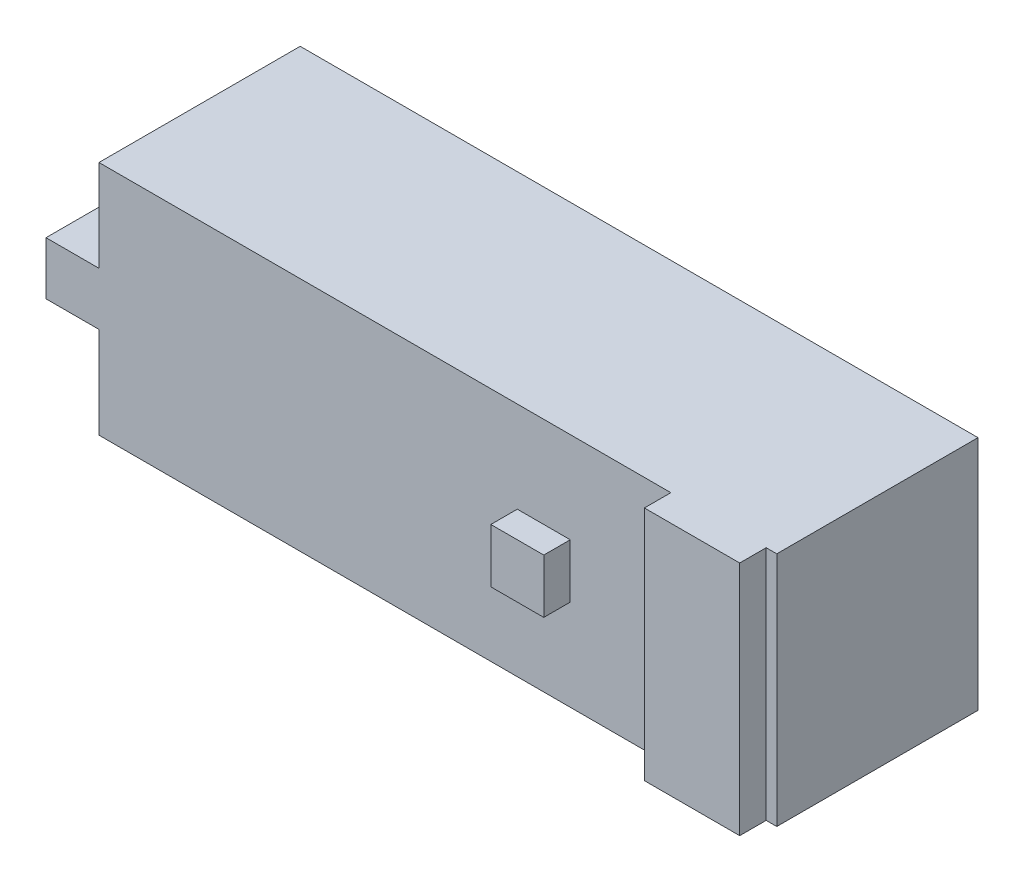
SolidWorks part; units mm, degrees
ref_plane "Front Plane" through (0, 0, 0) normal (0, 0, 1) x (1, 0, 0)
ref_plane "Top Plane" through (0, 0, 0) normal (0, 1, 0) x (1, 0, 0)
ref_plane "Right Plane" through (0, 0, 0) normal (1, 0, 0) x (0, 0, -1)
sketch "Sketch1" plane through (0, 0, 0) normal (0, 0, 1) x (1, 0, 0)
  line L0 (-32, 2.5) -> (-37, 2.5) construction
  line L1 (-32, 11.15) -> (32, 11.15) construction
  line L2 (-32, 11.15) -> (-32, -11.15) construction
  line L3 (-32, -11.15) -> (32, -11.15) construction
  line L4 (32, 11.15) -> (32, -11.15) construction
  line L5 (-32, 11.15) -> (32, -11.15) construction
  line L6 (-32, -11.15) -> (32, 11.15) construction
  line L7 (-23, 1.825) -> (-19, 1.825) construction
  line L8 (-23, 1.825) -> (-23, -1.825) construction
  line L9 (-23, -1.825) -> (-19, -1.825) construction
  line L10 (-19, 1.825) -> (-19, -1.825) construction
  line L11 (-23, 1.825) -> (-19, -1.825) construction
  line L12 (-23, -1.825) -> (-19, 1.825) construction
  line L13 (0, 0) -> (-44.9642, 0) construction
  line L14 (-32, -2.5) -> (-37, -2.5) construction
  line L15 (-37, 2.5) -> (-37, -2.5) construction
  line L16 (31, 11.15) -> (31, -11.15) construction
  line L17 (7.5, 2.55) -> (12.5, 2.55)
  line L18 (7.5, 2.55) -> (7.5, -2.55)
  line L19 (7.5, -2.55) -> (12.5, -2.55)
  line L20 (12.5, 2.55) -> (12.5, -2.55)
  line L21 (7.5, 2.55) -> (12.5, -2.55) construction
  line L22 (7.5, -2.55) -> (12.5, 2.55) construction
  line L23 (22, 11.15) -> (22, -11.15) construction
  circle A0 centre (-21, 0) radius 2.7075 construction
  circle A1 centre (-10, 0) radius 2.1
  point P0 (0, 0)
  point P6 (-21, 0)
  point P21 (10, 0)
  dimension "D8" = 4.2
  dimension "D1" = 64
  dimension "D2" = 22.3
  dimension "D3" = 11
  dimension "D4" = 3.65
  dimension "D5" = 4
  dimension "D6" = 2.5
  dimension "D7" = 5
  dimension "D9" = 11
  dimension "D10" = 20
  dimension "D11" = 5.1
  dimension "D12" = 5
  dimension "D13" = 63
  dimension "D14" = 9
sketch "Sketch2" plane through (0, 0, 0) normal (0, 0, 1) x (1, 0, 0)
  line L0 (-32, 11.15) -> (32, 11.15) construction
  line L1 (-32, 11.15) -> (-32, -11.15) construction
  line L2 (-32, -11.15) -> (32, -11.15) construction
  line L3 (32, 11.15) -> (32, -11.15) construction
  line L4 (-32, 11.15) -> (32, 11.15)
  line L5 (-32, 11.15) -> (-32, -11.15)
  line L6 (-32, -11.15) -> (32, -11.15)
  line L7 (32, 11.15) -> (32, -11.15)
  line L8 (-32, 2.5) -> (-37, 2.5) construction
  line L9 (-37, 2.5) -> (-37, -2.5) construction
  line L10 (-32, -2.5) -> (-37, -2.5) construction
  line L11 (-32, 2.5) -> (-37, 2.5)
  line L12 (-37, 2.5) -> (-37, -2.5)
  line L13 (-32, -2.5) -> (-37, -2.5)
extrude "Boss-Extrude1" add sketch "Sketch2" along normal blind 19 contours L7 L4 L5 L6 | L13 L5 L11 L12
sketch "Sketch3" plane through (0, 0, 0) normal (0, 0, 1) x (1, 0, 0)
  line L0 (-23, -1.825) -> (-19, -1.825) construction
  line L1 (-23, 1.825) -> (-19, 1.825) construction
  line L2 (-23, -1.825) -> (-19, -1.825)
  line L3 (-23, 1.825) -> (-19, 1.825)
  circle A0 centre (-21, 0) radius 2.7075 construction
  circle A1 centre (-21, 0) radius 2.7075
extrude "Boss-Extrude2" add sketch "Sketch3" against normal blind 8 contours L3 A1 L2
sketch "Sketch4" plane through (0, 0, 0) normal (0, 0, -1) x (-1, 0, 0)
  line L0 (-7.5, 2.55) -> (-12.5, 2.55) construction
  line L1 (-7.5, 2.55) -> (-7.5, -2.55) construction
  line L2 (-7.5, -2.55) -> (-12.5, -2.55) construction
  line L3 (-12.5, 2.55) -> (-12.5, -2.55) construction
  line L4 (-7.5, 2.55) -> (-12.5, 2.55)
  line L5 (-7.5, 2.55) -> (-7.5, -2.55)
  line L6 (-7.5, -2.55) -> (-12.5, -2.55)
  line L7 (-12.5, 2.55) -> (-12.5, -2.55)
  circle A0 centre (10, 0) radius 2.1 construction
  circle A1 centre (10, 0) radius 2.1
extrude "Boss-Extrude3" add sketch "Sketch4" along normal blind 2
sketch "Sketch5" plane through (0, 0, 19) normal (0, 0, 1) x (1, 0, 0)
  line L0 (12.5, 2.55) -> (12.5, -2.55) construction
  line L1 (-32, -11.15) -> (32, -11.15) construction
  line L2 (31, 11.15) -> (31, -11.15) construction
  line L4 (-32, 11.15) -> (32, 11.15) construction
  line L5 (7.5, 2.55) -> (12.5, 2.55) construction
  line L6 (7.5, 2.55) -> (7.5, -2.55) construction
  line L7 (7.5, -2.55) -> (12.5, -2.55) construction
  line L8 (-32, -11.15) -> (32, -11.15)
  line L9 (31, 11.15) -> (31, -11.15)
  line L11 (-32, 11.15) -> (32, 11.15)
  line L12 (12.5, 2.55) -> (12.5, -2.55)
  line L13 (7.5, 2.55) -> (12.5, 2.55)
  line L14 (7.5, 2.55) -> (7.5, -2.55)
  line L15 (7.5, -2.55) -> (12.5, -2.55)
  line L16 (22, 11.15) -> (22, -11.15) construction
  line L17 (22, 11.15) -> (22, -11.15)
  line M2 (32, 11.15) -> (-32, 11.15)
extrude "Boss-Extrude4" add sketch "Sketch5" along normal blind 2.5 contours L14 L15 L12 L13 | L17 L8 L9 M2
